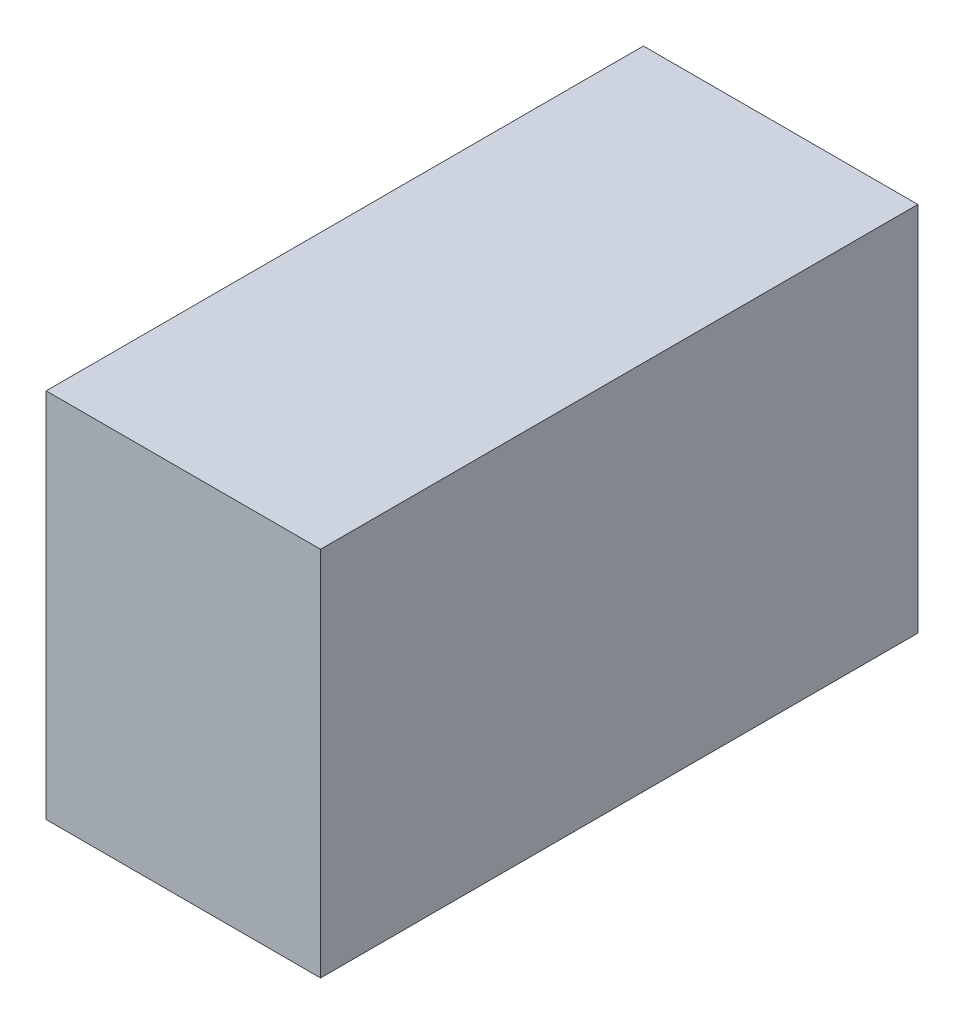
SolidWorks part; units mm, degrees
ref_plane "前视基准面" through (0, 0, 0) normal (0, 0, 1) x (1, 0, 0)
ref_plane "上视基准面" through (0, 0, 0) normal (0, 1, 0) x (1, 0, 0)
ref_plane "右视基准面" through (0, 0, 0) normal (1, 0, 0) x (0, 0, -1)
sketch "Sketch2" plane through (0, 0, 0) normal (0, 1, 0) x (1, 0, 0)
  line L1 (-101.75, 79.0875) -> (-67.75, 79.0875)
  line L2 (-101.75, 79.0875) -> (-101.75, 5.0875)
  line L3 (-101.75, 5.0875) -> (-67.75, 5.0875)
  line L4 (-67.75, 79.0875) -> (-67.75, 5.0875)
  line L5 (-101.75, 79.0875) -> (-67.75, 5.0875) construction
  line L6 (-101.75, 5.0875) -> (-67.75, 79.0875) construction
  point P0 (-84.75, 42.0875)
  dimension "D1" = 74
  dimension "D2" = 34
extrude "Boss-Extrude1" add sketch "Sketch2" along normal blind 46
